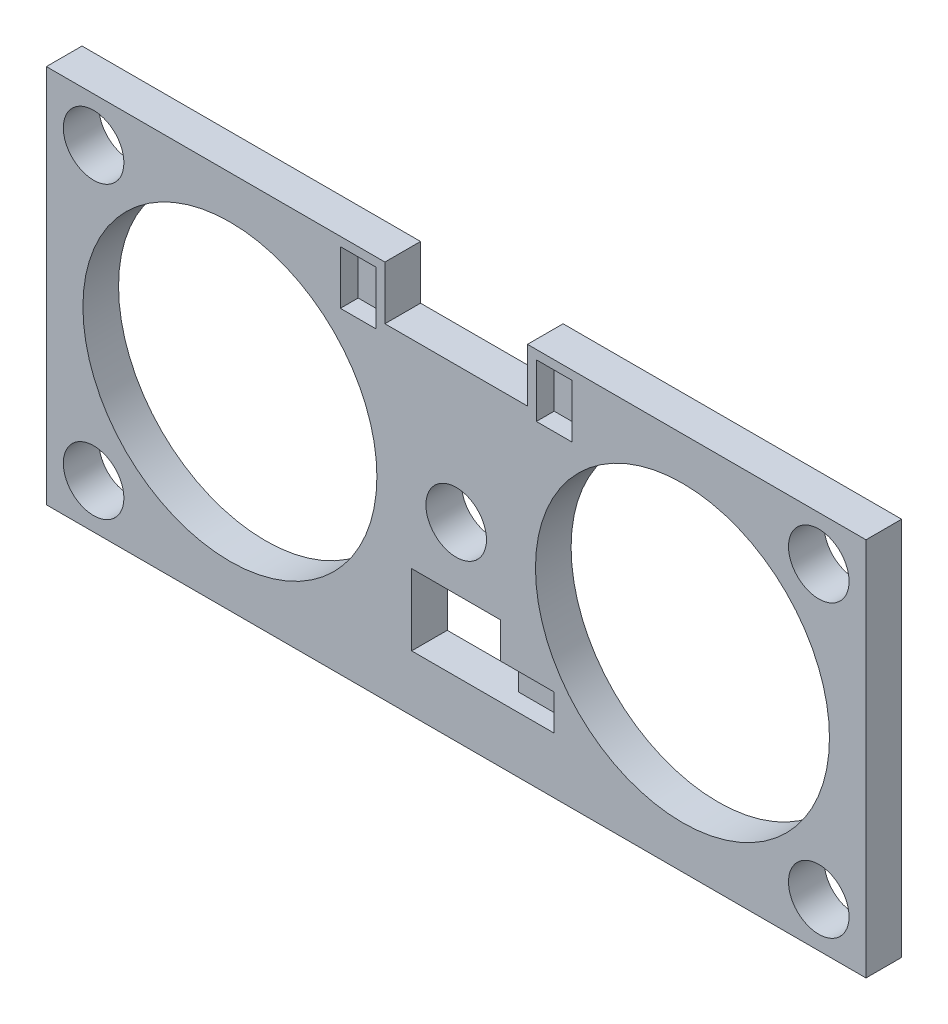
SolidWorks part; units mm, degrees
ref_plane "前基準面" through (0, 0, 0) normal (0, 0, 1) x (1, 0, 0)
ref_plane "上基準面" through (0, 0, 0) normal (0, 1, 0) x (1, 0, 0)
ref_plane "右基準面" through (0, 0, 0) normal (1, 0, 0) x (0, 0, -1)
sketch "草圖1" plane through (0, 0, 0) normal (0, 0, 1) x (1, 0, 0)
  line L1 (-23, -10.65) -> (23, -10.65)
  line L2 (-23, -10.65) -> (-23, 10.65)
  line L3 (-23, 10.65) -> (23, 10.65)
  line L4 (23, -10.65) -> (23, 10.65)
  line L5 (-23, -10.65) -> (23, 10.65) construction
  line L6 (-23, 10.65) -> (23, -10.65) construction
  point P0 (0, 0)
  dimension "D1" = 46
  dimension "D2" = 21.3
extrude "填料-伸長1" add sketch "草圖1" along normal blind 2
sketch "草圖2" plane through (0, 0, 2) normal (0, 0, 1) x (1, 0, 0)
  line L0 (-12.7, 0) -> (12.7, 0) construction
  circle A0 centre (-12.7, 0) radius 8.25
  circle A1 centre (12.7, 0) radius 8.25
  point P4 (0, 0)
  dimension "D1" = 25.4
  dimension "D2" = 16.5
extrude "除料-伸長1" cut sketch "草圖2" against normal through all
sketch "草圖3" plane through (0, 0, 2) normal (0, 0, 1) x (1, 0, 0)
  line L0 (0, 0) -> (0, 9.15) construction
  line L1 (23, 10.65) -> (-23, 10.65) construction
  line L2 (-4, 7.65) -> (4, 7.65)
  line L3 (-4, 7.65) -> (-4, 10.65)
  line L4 (-4, 10.65) -> (4, 10.65)
  line L5 (4, 7.65) -> (4, 10.65)
  line L6 (-4, 7.65) -> (4, 10.65) construction
  line L7 (-4, 10.65) -> (4, 7.65) construction
  dimension "D1" = 8
  dimension "D2" = 3
extrude "除料-伸長2" cut sketch "草圖3" against normal through all
sketch "草圖4" plane through (0, 0, 2) normal (0, 0, 1) x (1, 0, 0)
  line L0 (0, 0) -> (0, -5.5) construction
  line L2 (-2.5, -3.5) -> (2.5, -3.5)
  line L3 (-2.5, -3.5) -> (-2.5, -7.5)
  line L4 (-2.5, -7.5) -> (2.5, -7.5)
  line L5 (2.5, -3.5) -> (2.5, -7.5)
  line L6 (-2.5, -3.5) -> (2.5, -7.5) construction
  line L7 (-2.5, -7.5) -> (2.5, -3.5) construction
  dimension "D1" = 5
  dimension "D2" = 4
  dimension "D3" = 5.5
extrude "除料-伸長3" cut sketch "草圖4" against normal through all
sketch "草圖5" plane through (0, 0, 2) normal (0, 0, 1) x (1, 0, 0)
  line L0 (0, 0) -> (0, 8.65) construction
  line L1 (2.5, -7.5) -> (5.5, -7.5)
  line L2 (2.5, -7.5) -> (2.5, -5.5)
  line L3 (2.5, -5.5) -> (5.5, -5.5)
  line L4 (5.5, -7.5) -> (5.5, -5.5)
  line L5 (-5.5, 8.65) -> (5.5, 8.65) construction
  line L6 (23, 10.65) -> (4, 10.65) construction
  line L7 (-4.5, 10.15) -> (-6.5, 10.15)
  line L8 (-4.5, 10.15) -> (-4.5, 7.15)
  line L9 (-4.5, 7.15) -> (-6.5, 7.15)
  line L10 (-6.5, 10.15) -> (-6.5, 7.15)
  line L11 (-4.5, 10.15) -> (-6.5, 7.15) construction
  line L12 (-4.5, 7.15) -> (-6.5, 10.15) construction
  line L13 (6.5, 10.15) -> (4.5, 10.15)
  line L14 (6.5, 10.15) -> (6.5, 7.15)
  line L15 (6.5, 7.15) -> (4.5, 7.15)
  line L16 (4.5, 10.15) -> (4.5, 7.15)
  line L17 (6.5, 10.15) -> (4.5, 7.15) construction
  line L18 (6.5, 7.15) -> (4.5, 10.15) construction
  point P10 (0, 8.65)
  dimension "D1" = 2
  dimension "D2" = 3
  dimension "D3" = 2
  dimension "D4" = 3
  dimension "D5" = 11
  dimension "D6" = 0.5
extrude "除料-伸長4" cut sketch "草圖5" against normal blind 1
hole_wizard "M3 餘隙孔1" positions "草圖6" profile "草圖7" hole size "M3" standard "Ansi Metric" end condition through all
sketch "草圖6" plane through (0, 0, 2) normal (0, 0, 1) x (1, 0, 0)
  line L1 (-20.35, -8.15) -> (20.35, -8.15) construction
  line L2 (-20.35, -8.15) -> (-20.35, 8.15) construction
  line L3 (-20.35, 8.15) -> (20.35, 8.15) construction
  line L4 (20.35, -8.15) -> (20.35, 8.15) construction
  line L5 (-20.35, -8.15) -> (20.35, 8.15) construction
  line L6 (-20.35, 8.15) -> (20.35, -8.15) construction
  point P0 (0, 0)
  point P1 (20.35, 8.15)
  point P112 (-20.35, -8.15)
  point P113 (-20.35, 8.15)
  point P114 (20.35, -8.15)
  dimension "D1" = 16.3
  dimension "D2" = 40.7
sketch "草圖7" plane through (0, 0, 2) normal (1, 0, 0) x (0, -1, 0)
  line L0 (0, 0) -> (0, 2)
  line L1 (0, 2) -> (1.7, 2)
  line L2 (1.7, 2) -> (1.7, 0)
  line L5 (1.7, 0) -> (0, 0)
  line L11 (0, -6.35) -> (0, 107.95) construction
  dimension "貫穿孔直徑" = 3.4
  dimension "貫穿孔深度" = 2
